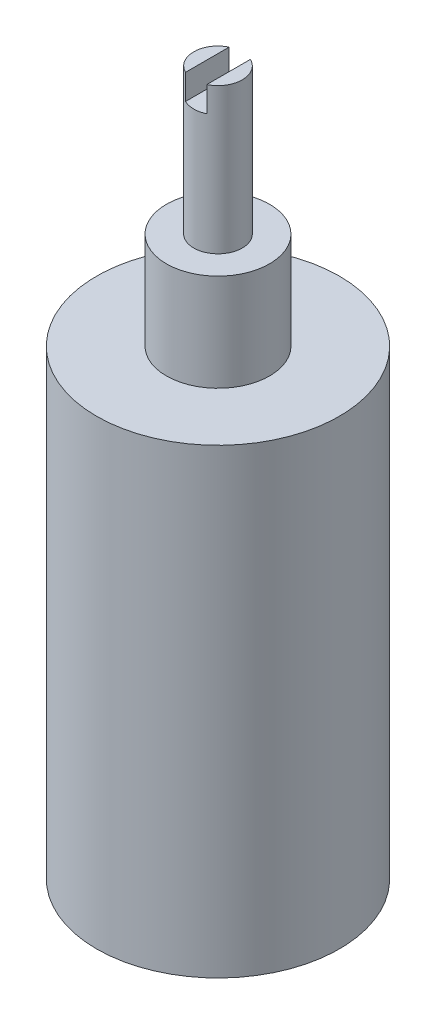
SolidWorks part; units mm, degrees
ref_plane "Front Plane" through (0, 0, 0) normal (0, 0, 1) x (1, 0, 0)
ref_plane "Top Plane" through (0, 0, 0) normal (0, 1, 0) x (1, 0, 0)
ref_plane "Right Plane" through (0, 0, 0) normal (1, 0, 0) x (0, 0, -1)
sketch "Sketch1" plane through (0, 0, 0) normal (0, 1, 0) x (1, 0, 0)
  circle A0 centre (0, 0) radius 10
  dimension "D1" = 20
extrude "Boss-Extrude1" add sketch "Sketch1" along normal mid plane 38
sketch "Sketch2" plane through (0, 19, 0) normal (0, 1, 0) x (1, 0, 0)
  circle A0 centre (0, 0) radius 4.25
  dimension "D1" = 8.5
extrude "Boss-Extrude2" add sketch "Sketch2" along normal blind 8
sketch "Sketch3" plane through (0, 27, 0) normal (0, 1, 0) x (1, 0, 0)
  circle A0 centre (0, 0) radius 2
  dimension "D1" = 4
extrude "Boss-Extrude3" add sketch "Sketch3" along normal blind 12
sketch "Sketch4" plane through (0, 0, 0) normal (0, 0, 1) x (1, 0, 0)
  line L0 (0, 39) -> (0, 27) construction
  line L1 (2, 39) -> (-2, 39) construction
  line L2 (4.25, 27) -> (-4.25, 27) construction
  line L3 (-0.875, 41.0821) -> (-0.875, 36.9179)
  line L4 (-0.875, 41.0821) -> (0.875, 41.0821)
  line L5 (-0.875, 36.9179) -> (0.875, 36.9179)
  line L6 (0.875, 41.0821) -> (0.875, 36.9179)
  line L7 (0, 36.9179) -> (0, 41.0821) construction
  line L8 (-0.875, 39) -> (0.875, 39) construction
extrude "Cut-Extrude1" cut sketch "Sketch4" against normal through all both and the other way through all
